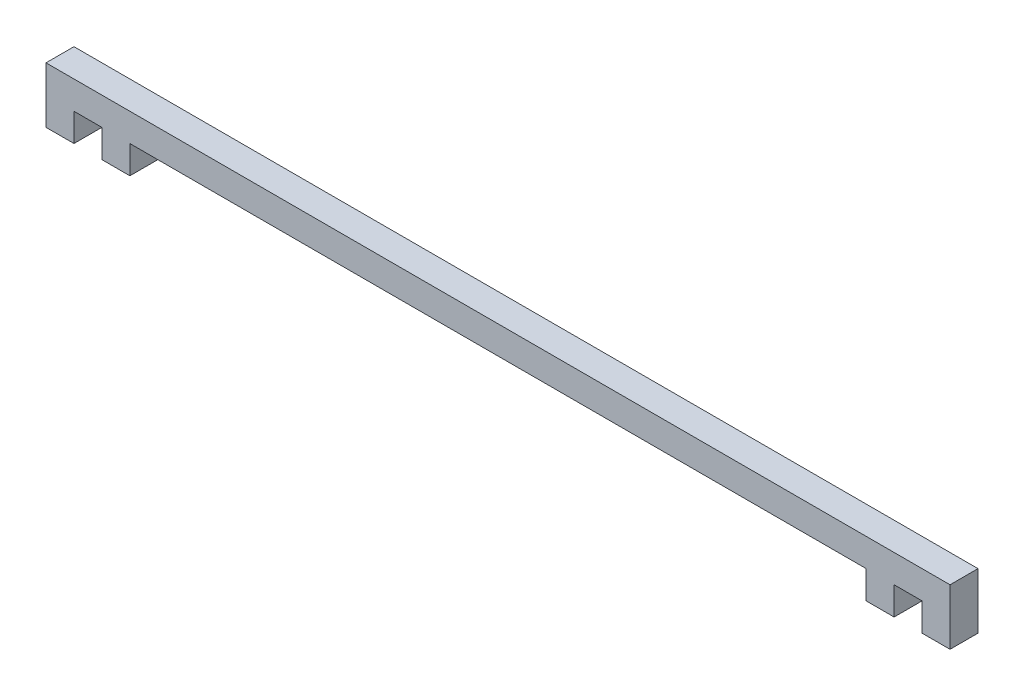
SolidWorks part; units mm, degrees
ref_plane "Alzado" through (0, 0, 0) normal (0, 0, 1) x (1, 0, 0)
ref_plane "Planta" through (0, 0, 0) normal (0, 1, 0) x (1, 0, 0)
ref_plane "Vista lateral" through (0, 0, 0) normal (1, 0, 0) x (0, 0, -1)
sketch "Croquis2" plane through (0, 0, 0) normal (0, 0, 1) x (1, 0, 0)
  line L0 (-43.4121, 0) -> (35.5879, 0)
  line L1 (35.5879, 0) -> (35.5879, -3)
  line L2 (35.5879, -3) -> (38.5879, -3)
  line L3 (38.5879, -3) -> (38.5879, 0)
  line L4 (38.5879, 0) -> (41.5879, 0)
  line L5 (41.5879, 0) -> (41.5879, -3)
  line L6 (41.5879, -3) -> (44.5879, -3)
  line L7 (44.5879, -3) -> (44.5879, 3)
  line L8 (44.5879, 3) -> (-52.4121, 3)
  line L9 (-52.4121, 3) -> (-52.4121, -3)
  line L10 (-52.4121, -3) -> (-49.4121, -3)
  line L11 (-49.4121, -3) -> (-49.4121, 0)
  line L12 (-49.4121, 0) -> (-46.4121, 0)
  line L13 (-46.4121, 0) -> (-46.4121, -3)
  line L14 (-46.4121, -3) -> (-43.4121, -3)
  line L15 (-43.4121, -3) -> (-43.4121, 0)
  point P18 (0, 0)
  dimension "D1" = 79
  dimension "D2" = 3
  dimension "D3" = 3
  dimension "D4" = 3
  dimension "D5" = 3
  dimension "D6" = 3
  dimension "D7" = 3
  dimension "D8" = 3
  dimension "D9" = 3
  dimension "D10" = 3
  dimension "D11" = 3
  dimension "D12" = 3
extrude "Saliente-Extruir1" add sketch "Croquis2" along normal blind 3
